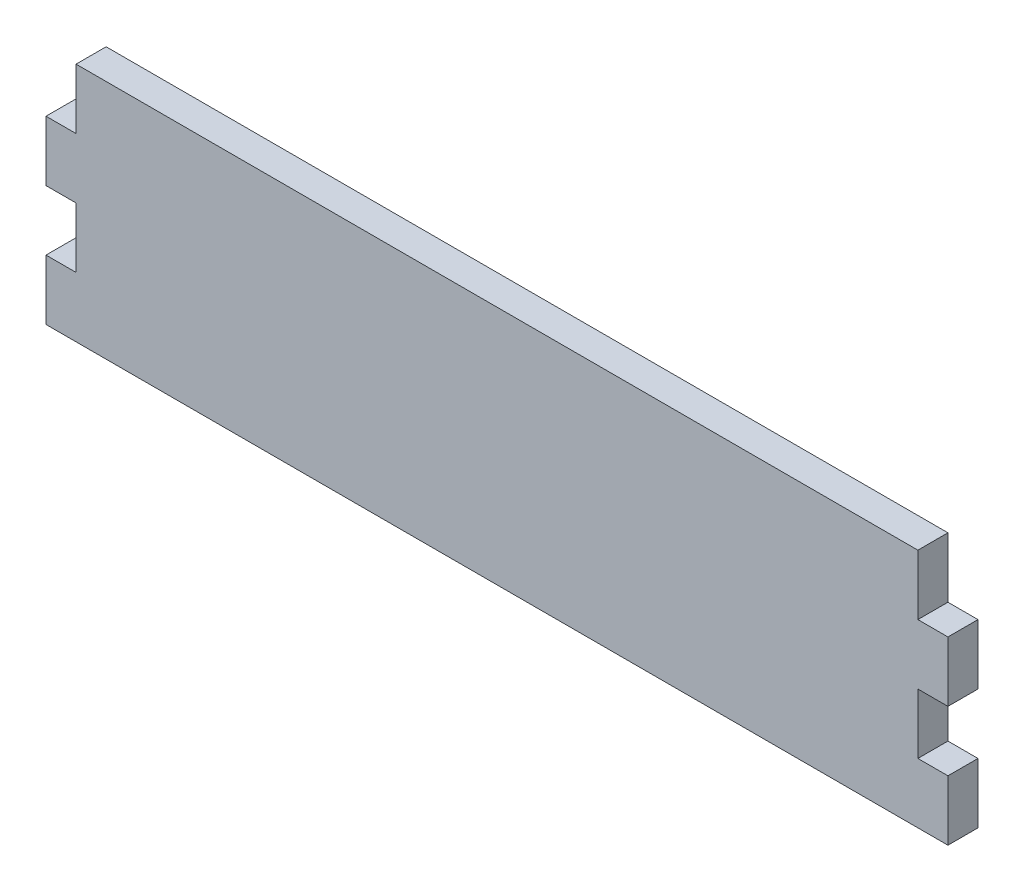
SolidWorks part; units mm, degrees
ref_plane "Front Plane" through (0, 0, 0) normal (0, 0, 1) x (1, 0, 0)
ref_plane "Top Plane" through (0, 0, 0) normal (0, 1, 0) x (1, 0, 0)
ref_plane "Right Plane" through (0, 0, 0) normal (1, 0, 0) x (0, 0, -1)
sketch "Sketch1" plane through (0, 0, 0) normal (0, 0, 1) x (1, 0, 0)
  line L1 (-95.25, 25.4) -> (95.25, 25.4)
  line L2 (-95.25, 25.4) -> (-95.25, -25.4)
  line L3 (-95.25, -25.4) -> (95.25, -25.4)
  line L4 (95.25, 25.4) -> (95.25, -25.4)
  line L5 (-95.25, 25.4) -> (95.25, -25.4) construction
  line L6 (-95.25, -25.4) -> (95.25, 25.4) construction
  point P1 (0, 0)
  dimension "D1" = 50.8
  dimension "D2" = 190.5
extrude "Boss-Extrude1" add sketch "Sketch1" along normal blind 6.35
sketch "Sketch2" plane through (0, 0, 6.35) normal (0, 0, 1) x (1, 0, 0)
  line L0 (95.25, -25.4) -> (95.25, 25.4) construction
  line L1 (95.25, -12.7) -> (88.9, -12.7)
  line L2 (95.25, -12.7) -> (95.25, 0)
  line L3 (95.25, 0) -> (88.9, 0)
  line L4 (88.9, -12.7) -> (88.9, 0)
  dimension "D1" = 6.35
  dimension "D2" = 12.7
  dimension "D3" = 12.7
extrude "Cut-Extrude1" cut sketch "Sketch2" against normal through all
pattern_linear "LPattern1" count 2 spacing 25.4 along (0, 1, 0) of "Cut-Extrude1"
mirror "Mirror1" about plane through (0, 0, 0) normal (1, 0, 0) of "LPattern1", "Cut-Extrude1"
